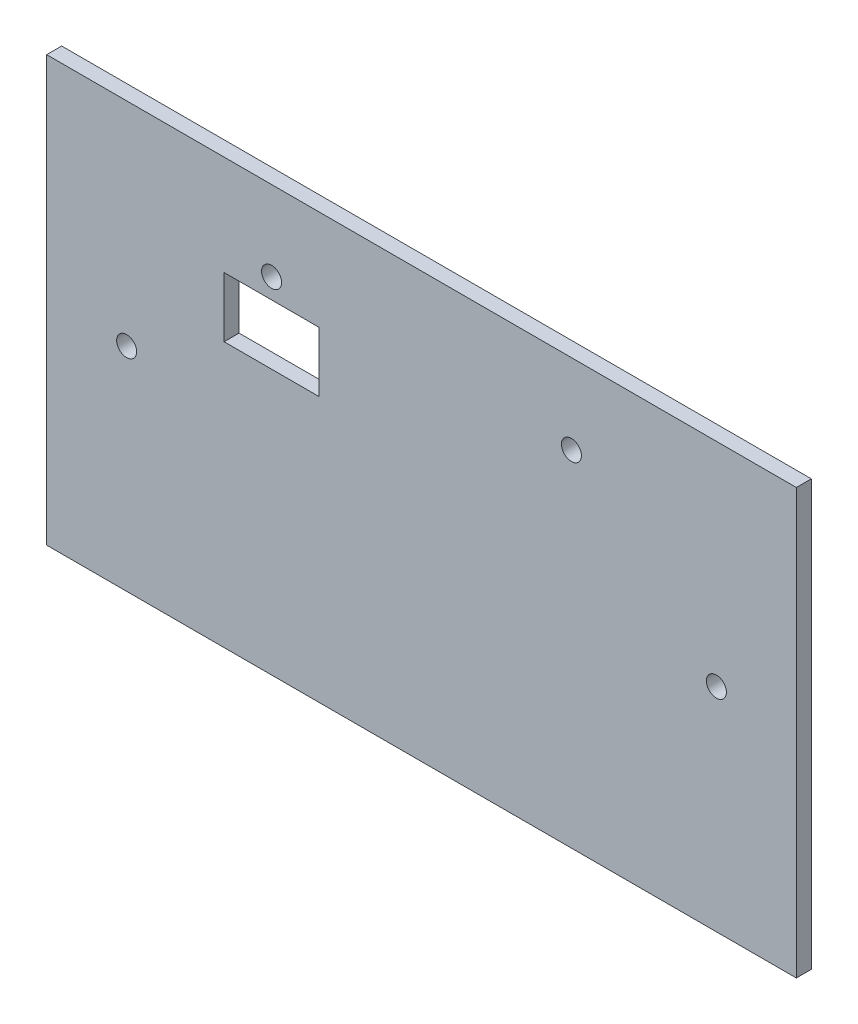
SolidWorks part; units mm, degrees
ref_plane "Front" through (0, 0, 0) normal (0, 0, 1) x (1, 0, 0)
ref_plane "Top" through (0, 0, 0) normal (0, 1, 0) x (1, 0, 0)
ref_plane "Right" through (0, 0, 0) normal (1, 0, 0) x (0, 0, -1)
sketch "Sketch1" plane through (0, 0, 0) normal (0, 0, 1) x (1, 0, 0)
  line L1 (75, 42.5) -> (-75, 42.5)
  line L2 (75, 42.5) -> (75, -42.5)
  line L3 (75, -42.5) -> (-75, -42.5)
  line L4 (-75, 42.5) -> (-75, -42.5)
  line L5 (75, 42.5) -> (-75, -42.5) construction
  line L6 (75, -42.5) -> (-75, 42.5) construction
  point P0 (0, 0)
  dimension "D1" = 150
  dimension "D2" = 85
extrude "Boss-Extrude1" add sketch "Sketch1" along normal blind 3 contours L4 L3 L2 L1
sketch "Sketch2" plane through (0, 0, 3) normal (0, 0, 1) x (1, 0, 0)
  line L1 (75, 42.5) -> (-75, 42.5) construction
  circle A0 centre (-30, 26.5) radius 2
  dimension "D1" = 4
  dimension "D2" = 16
  dimension "D3" = 30
extrude "Cut-Extrude1" cut sketch "Sketch2" against normal up to next (3 mm away) contours A0
mirror "Mirror1" about plane through (0, 0, 0) normal (1, 0, 0) of "Cut-Extrude1"
sketch "Sketch3" plane through (0, 0, 3) normal (0, 0, 1) x (1, 0, 0)
  line L0 (-75, 42.5) -> (-75, -42.5) construction
  circle A0 centre (-59, 0) radius 2
  point P5 (-75, 0)
  dimension "D1" = 4
  dimension "D2" = 16
extrude "Cut-Extrude2" cut sketch "Sketch3" against normal up to next (3 mm away)
mirror "Mirror2" about plane through (0, 0, 0) normal (1, 0, 0) of "Cut-Extrude2"
sketch "Sketch5" plane through (0, 0, 3) normal (0, 0, 1) x (1, 0, 0)
  line L1 (-39.5, 22.5) -> (-20.5, 22.5)
  line L2 (-39.5, 22.5) -> (-39.5, 10.5)
  line L3 (-39.5, 10.5) -> (-20.5, 10.5)
  line L4 (-20.5, 22.5) -> (-20.5, 10.5)
  line L5 (-39.5, 22.5) -> (-20.5, 10.5) construction
  line L6 (-39.5, 10.5) -> (-20.5, 22.5) construction
  line L7 (75, 42.5) -> (-75, 42.5) construction
  line L8 (-75, 42.5) -> (-75, -42.5) construction
  point P0 (-30, 16.5)
  dimension "D1" = 19
  dimension "D2" = 12
  dimension "D3" = 45
  dimension "D4" = 20
extrude "Cut-Extrude4" cut sketch "Sketch5" against normal up to next contours L3 L4 L1 L2
